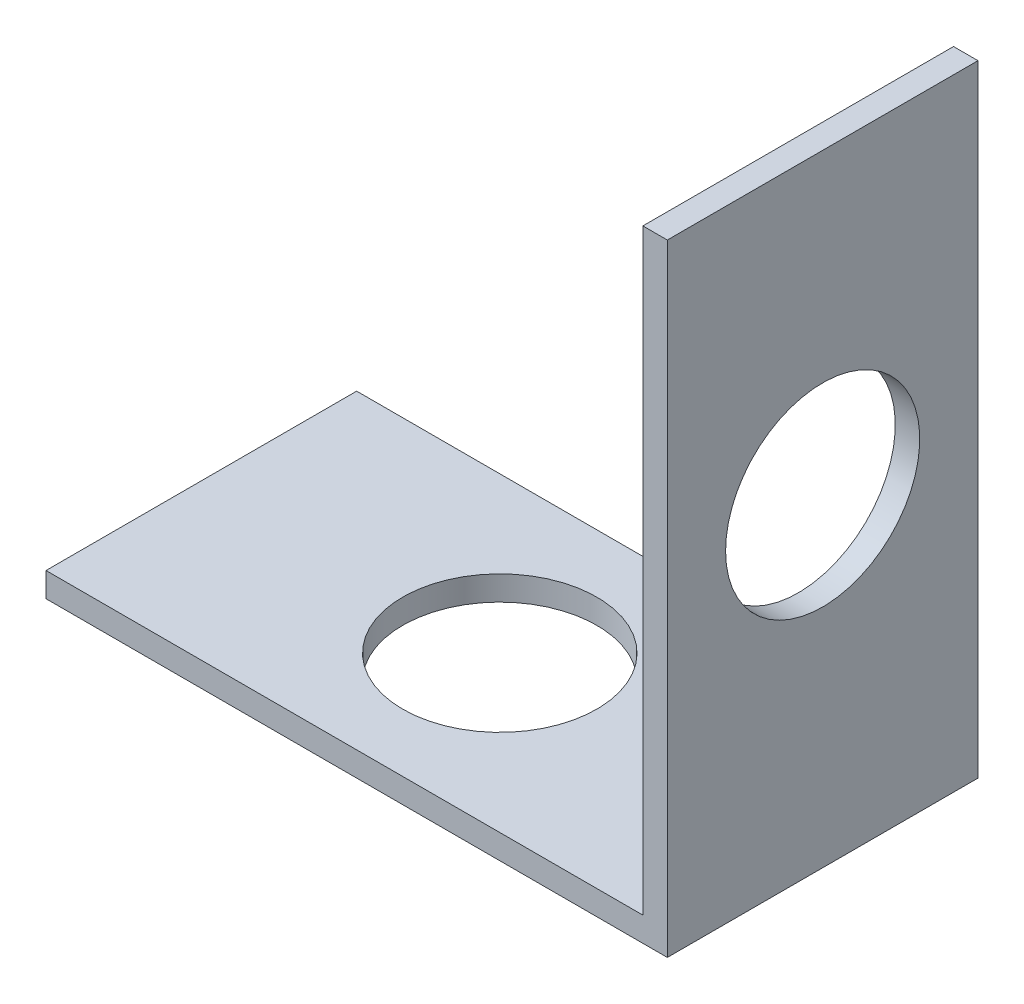
SolidWorks part; units mm, degrees
material "6061 Alloy"
ref_plane "Front Plane" through (0, 0, 0) normal (0, 0, 1) x (1, 0, 0)
ref_plane "Top Plane" through (0, 0, 0) normal (0, 1, 0) x (1, 0, 0)
ref_plane "Right Plane" through (0, 0, 0) normal (1, 0, 0) x (0, 0, -1)
sketch "Sketch1" plane through (0, 0, 0) normal (0, 0, 1) x (1, 0, 0)
  line L0 (0, 0) -> (0, 25.4)
  line L1 (0, 0) -> (-25.4, 0)
  line L2 (-1, 1) -> (-25.4, 1)
  line L3 (-1, 1) -> (-1, 25.4)
  line L4 (-25.4, 1) -> (-25.4, 0)
  line L5 (-1, 25.4) -> (0, 25.4)
  dimension "D1" = 1
  dimension "D2" = 25.4
  dimension "D3" = 25.4
extrude "Boss-Extrude1" add sketch "Sketch1" along normal mid plane 12.7
sketch "Sketch2" plane through (-1, 0, 0) normal (-1, 0, 0) x (0, 0, 1)
  line L0 (0, 25.4) -> (0, 1) construction
  line L1 (6.35, 25.4) -> (-6.35, 25.4) construction
  line L2 (6.35, 1) -> (-6.35, 1) construction
  line L3 (-6.35, 13.2) -> (6.35, 13.2) construction
  line L4 (-6.35, 25.4) -> (-6.35, 1) construction
  line L5 (6.35, 25.4) -> (6.35, 1) construction
  point P0 (0, 13.2)
  point P15 (0, 0)
hole_wizard "5/16 (0.3125) Diameter Hole1" positions "Sketch3" profile "Sketch4" hole size "5/16" standard "ANSI Inch" end condition through all
sketch "Sketch3" plane through (-1, 0, 0) normal (-1, 0, 0) x (0, 0, 1)
  point P0 (0, 13.2)
sketch "Sketch4" plane through (-1, 13.2, 0) normal (0, 1, 0) x (0, 0, 1)
  line L0 (0, 0) -> (0, 1)
  line L1 (0, 1) -> (3.9688, 1)
  line L2 (3.9688, 1) -> (3.9688, 0)
  line L5 (3.9688, 0) -> (0, 0)
  line L11 (0, -6.35) -> (0, 107.95) construction
  dimension "Thru Hole Dia." = 7.9375
  dimension "Thru Hole Depth" = 1
sketch "Sketch5" plane through (0, 1, 0) normal (0, 1, 0) x (1, 0, 0)
  line L0 (-13.2, 6.35) -> (-13.2, -6.35) construction
  line L1 (-1, 6.35) -> (-25.4, 6.35) construction
  line L2 (-1, -6.35) -> (-25.4, -6.35) construction
  line L3 (-25.4, 0) -> (-1, 0) construction
  line L4 (-25.4, -6.35) -> (-25.4, 6.35) construction
  point P11 (-13.2, 0)
hole_wizard "5/16 (0.3125) Diameter Hole2" positions "3DSketch1" profile "Sketch6" hole size "5/16" standard "ANSI Inch" end condition through all
sketch3d "3DSketch1"
  point P0 (-13.2, 1, 0)
sketch "Sketch6" plane through (-13.2, 1, 0) normal (1, 0, 0) x (0, 0, 1)
  line L0 (0, 0) -> (0, 1)
  line L1 (0, 1) -> (3.9688, 1)
  line L2 (3.9688, 1) -> (3.9687, 0)
  line L5 (3.9687, 0) -> (0, 0)
  line L11 (0, -6.35) -> (0, 107.95) construction
  dimension "Thru Hole Dia." = 7.9375
  dimension "Thru Hole Depth" = 1
